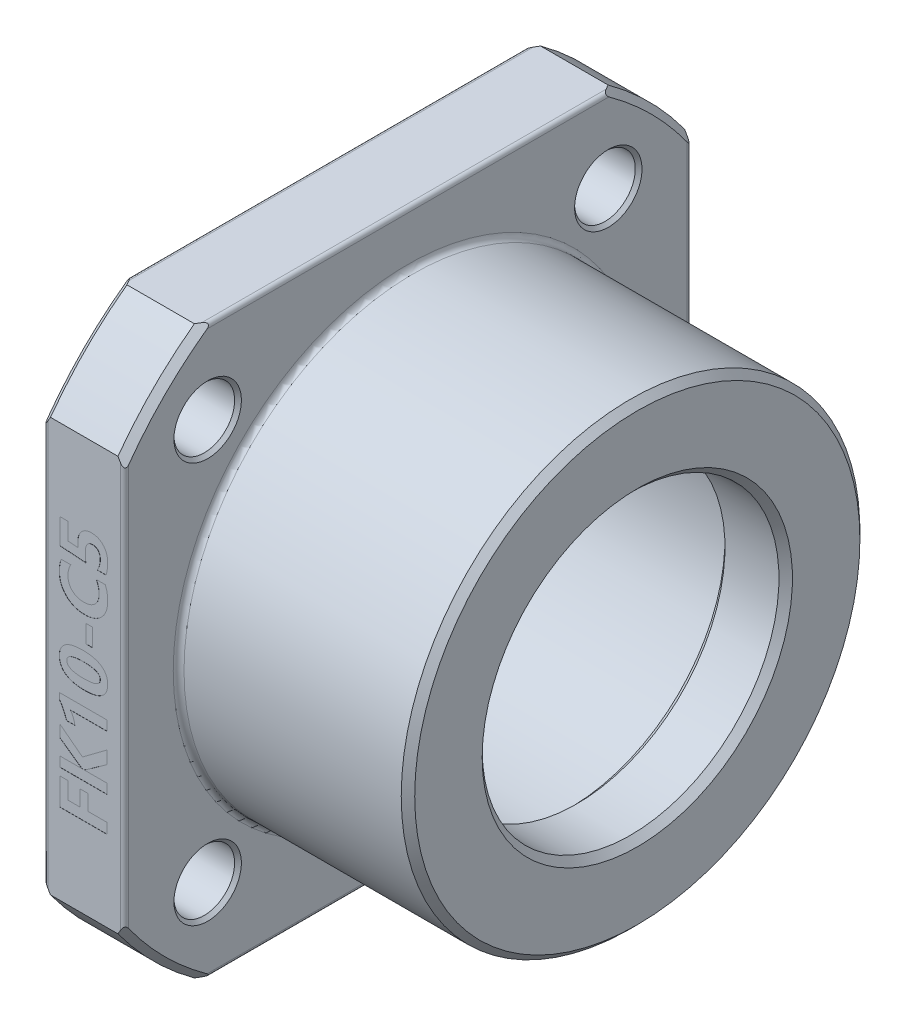
SolidWorks part; units mm, degrees
material "Простая углеродистая сталь"
ref_plane "Спереди  XY" through (0, 0, 0) normal (0, 0, 1) x (1, 0, 0)
ref_plane "Сверху  XZ" through (0, 0, 0) normal (0, 1, 0) x (1, 0, 0)
ref_plane "Справа  ZY" through (0, 0, 0) normal (1, 0, 0) x (0, 0, -1)
sketch "Эскиз1" plane through (0, 0, 0) normal (0, 0, 1) x (1, 0, 0)
  line L0 (0, 0) -> (23, 0) construction
  line L1 (22.5, 11) -> (18.5, 11)
  line L2 (18, 11.5) -> (18, 12.6)
  line L3 (17.6, 13) -> (0.5, 13)
  line L4 (0, 13.5) -> (0, 25.5)
  line L5 (0.5, 26) -> (5.5, 26)
  line L6 (6, 25.5) -> (6, 17.4)
  line L7 (6.4, 17) -> (22.5, 17)
  line L8 (23, 16.5) -> (23, 11.5)
  line L9 (0.5, 13) -> (0, 13.5)
  line L10 (23, 11.5) -> (22.5, 11)
  line L11 (18.5, 11) -> (18, 11.5)
  line L12 (22.5, 17) -> (23, 16.5)
  line L13 (5.5, 26) -> (6, 25.5)
  line L14 (0, 25.5) -> (0.5, 26)
  arc A0 (18, 12.6) -> (17.6, 13) centre (17.6, 12.6) ccw
  arc A1 (6, 17.4) -> (6.4, 17) centre (6.4, 17.4) ccw
  point P3 (23, 11)
  point P4 (18, 11)
  point P5 (0, 0)
  point P7 (0, 13)
  point P8 (0, 26)
  point P9 (6, 26)
  point P11 (23, 17)
  point P12 (0, 0)
  point P15 (18, 13)
  dimension "D8" = 0.4
  dimension "D1" = 23
  dimension "D2" = 11
  dimension "D3" = 18
  dimension "D4" = 13
  dimension "D5" = 17
  dimension "D6" = 26
  dimension "D7" = 6
revolve "Повернуть1" add sketch "Эскиз1" angle 360 about L0
sketch "Эскиз2" plane through (0, 0, 0) normal (-1, 0, 0) x (0, 0, 1)
  line L0 (0, 0) -> (0, 21) construction
  line L1 (-15.3297, 21) -> (15.3297, 21)
  line L2 (21, 15.3297) -> (21, -15.3297)
  line L3 (0, 0) -> (21, 0) construction
  line L4 (15.3297, -21) -> (-15.3297, -21)
  line L5 (0, 0) -> (0, -21) construction
  line L6 (-21, -15.3297) -> (-21, 15.3297)
  line L7 (0, 0) -> (-21, 0) construction
  circle A1 centre (0, 0) radius 26 construction
  arc A3 (-21, 15.3297) -> (-21, -15.3297) centre (0, 0) ccw
  arc A4 (15.3297, 21) -> (-15.3297, 21) centre (0, 0) ccw
  arc A5 (21, -15.3297) -> (21, 15.3297) centre (0, 0) ccw
  arc A6 (-15.3297, -21) -> (15.3297, -21) centre (0, 0) ccw
  point P9 (0, 21)
  point P21 (0, 0)
  dimension "D1" = 21
  dimension "D2" = 4
extrude "Вырез-Вытянуть1" cut sketch "Эскиз2" against normal up to next
hole_wizard "Диаметр отверстия Ø4.5 (4.5)1" positions "Эскиз3" profile "Эскиз4" hole size "Ø4.5" standard "Ansi Metric" end condition up to next
sketch "Эскиз3" plane through (0, 0, 0) normal (-1, 0, 0) x (0, 0, 1)
  line L0 (0, 0) -> (0, 21) construction
  line L1 (-14.4655, 21) -> (14.4655, 21) construction
  line L3 (-14.8492, -14.8492) -> (14.8492, 14.8492) construction
  line L5 (-14.8492, 14.8492) -> (14.8492, -14.8492) construction
  point P0 (-14.8492, 14.8492)
  point P2 (14.8492, 14.8492)
  point P4 (14.8492, -14.8492)
  point P6 (-14.8492, -14.8492)
  dimension "D1" = 42
  dimension "D2" = 45
  dimension "D3" = 90
sketch "Эскиз4" plane through (0, 14.8492, -14.8492) normal (0, 1, 0) x (0, 0, 1)
  line L0 (0, 0) -> (0, 6)
  line L1 (0, 6) -> (2.5, 6)
  line L2 (2.25, 5.75) -> (2.25, 0.25)
  line L3 (2.25, 0.25) -> (2.5, 0)
  line L5 (2.5, 0) -> (0, 0)
  line L6 (-2.25, 0.25) -> (-2.5, 0) construction
  line L7 (2.5, 6) -> (2.25, 5.75)
  line L8 (-2.5, 6) -> (-2.25, 5.75) construction
  line L11 (0, -6.35) -> (0, 107.95) construction
  dimension "Диаметр сквозного отверстия" = 4.5
  dimension "Глубина сквозного отверстия" = 6
  dimension "Диаметр передней зенковки" = 5
  dimension "Угол передней зенковки" = 90
  dimension "Диаметр задней зенковки" = 5
  dimension "Угол задней зенковки" = 90
hole_wizard "Отверстие обработанное метчиком M4x0.71" positions "Эскиз5" profile "Эскиз6" tap size "M4x0.7" standard "Ansi Metric"
sketch "Эскиз5" plane through (0, 0, 0) normal (-1, 0, 0) x (0, 0, 1)
  line L0 (0, 0) -> (0, 21) construction
  line L1 (-14.4655, 21) -> (14.4655, 21) construction
  line L3 (-5.8143, -15.9748) -> (5.8143, 15.9748) construction
  line L5 (-15.9748, 5.8143) -> (15.9748, -5.8143) construction
  point P0 (5.8143, 15.9748)
  point P2 (-5.8143, -15.9748)
  point P4 (-15.9748, 5.8143)
  point P6 (15.9748, -5.8143)
  dimension "D1" = 34
  dimension "D2" = 90
  dimension "D3" = 20
sketch "Эскиз6" plane through (0, 15.9748, 5.8143) normal (0, 1, 0) x (0, 0, 1)
  line L0 (0, 0) -> (0, 5.9914)
  line L1 (0, 5.9914) -> (1.65, 5)
  line L2 (1.65, 5) -> (1.65, 0.45)
  line L3 (1.65, 0.45) -> (2.1, 0)
  line L5 (2.1, 0) -> (0, 0)
  line L6 (-1.65, 0.45) -> (-2.1, 0) construction
  line L10 (0, 5.9914) -> (-1.65, 5) construction
  line L11 (0, -6.35) -> (0, 107.95) construction
  dimension "Диаметр сверла" = 3.3
  dimension "Глубина сверла" = 5
  dimension "Диаметр передней зенковки" = 4.2
  dimension "Угол передней зенковки" = 90
  dimension "Угол заточки сверла" = 118
cosmetic thread "Отверстие резьбы1" parameters "D1"=4, "D2"=4
cosmetic thread "Отверстие резьбы2" parameters "D1"=4, "D2"=4
cosmetic thread "Отверстие резьбы3" parameters "D1"=4, "D2"=4
cosmetic thread "Отверстие резьбы4" parameters "D1"=4, "D2"=4
fillet "Скругление1" radius 0.3 8 edges at (0, -21, 0) (0, 0, 21) (6, 0, 21) (6, -21, 0) (6, 21, 0) (6, 0, -21) (0, 0, -21) (0, 21, 0)
sketch "Эскиз7" plane through (0, 0, 21) normal (0, 0, 1) x (1, 0, 0)
  line L0 (4.7, -15.3297) -> (4.7, 15.3297) construction
  line L1 (5.5, -15.3297) -> (0.5, -15.3297) construction
  line L2 (5.5, 15.3297) -> (0.5, 15.3297) construction
  line L3 (5.7, -14.988) -> (5.7, 14.988) construction
  text T0 "FK10-C5" font "@Microsoft YaHei" height 3.5
  dimension "D1" = 1
extrude "Вырез-Вытянуть2" cut sketch "Эскиз7" against normal blind 0.01
